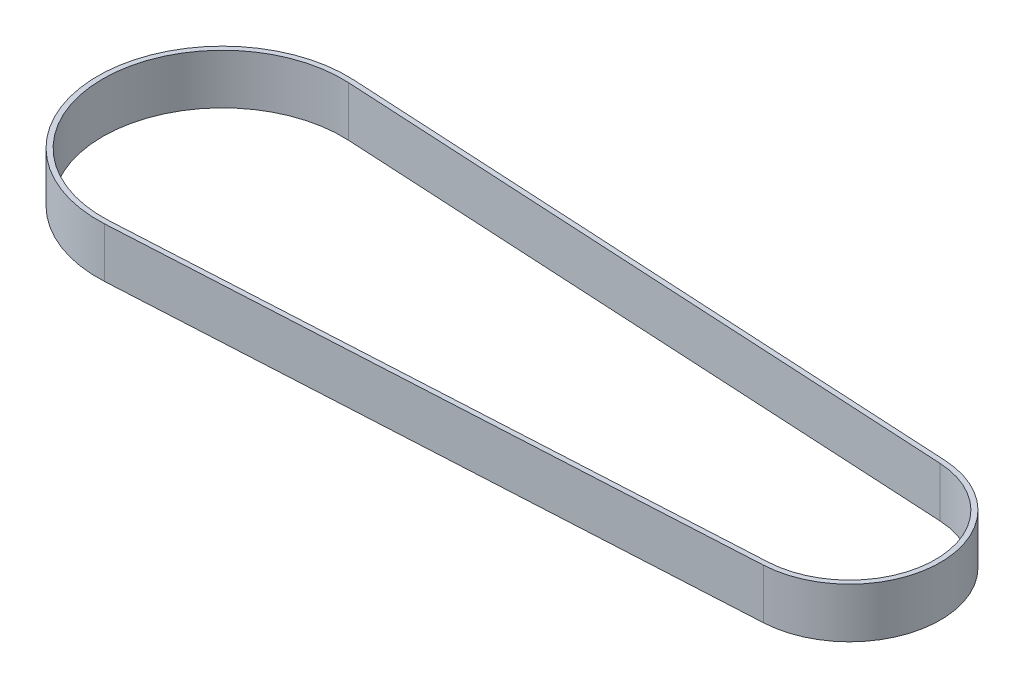
SolidWorks part; units mm, degrees
material "BUTYL"
ref_plane "Front Plane" through (0, 0, 0) normal (0, 0, 1) x (1, 0, 0)
ref_plane "Top Plane" through (0, 0, 0) normal (0, 1, 0) x (1, 0, 0)
ref_plane "Right Plane" through (0, 0, 0) normal (1, 0, 0) x (0, 0, -1)
sketch "Sketch1" plane through (0, 0, 0) normal (0, 1, 0) x (1, 0, 0)
  line L0 (0, 0) -> (125.6, 0) construction
  line L1 (1.2994, 23.9648) -> (126.5312, 17.1748)
  line L2 (1.3535, 24.9633) -> (126.5854, 18.1733)
  line L3 (1.3535, -24.9633) -> (126.5854, -18.1733)
  line L4 (1.2994, -23.9648) -> (126.5312, -17.1748)
  arc A0 (1.2994, 23.9648) -> (1.2994, -23.9648) centre (0, 0) ccw
  arc A1 (126.5312, -17.1748) -> (126.5312, 17.1748) centre (125.6, 0) ccw
  arc A2 (126.5854, -18.1733) -> (126.5854, 18.1733) centre (125.6, 0) ccw
  arc A3 (1.3535, 24.9633) -> (1.3535, -24.9633) centre (0, 0) ccw
  dimension "D1" = 48
  dimension "D3" = 34.4
  dimension "D2" = 125.6
  dimension "D4" = 1
extrude "Boss-Extrude1" add sketch "Sketch1" along normal blind 10
